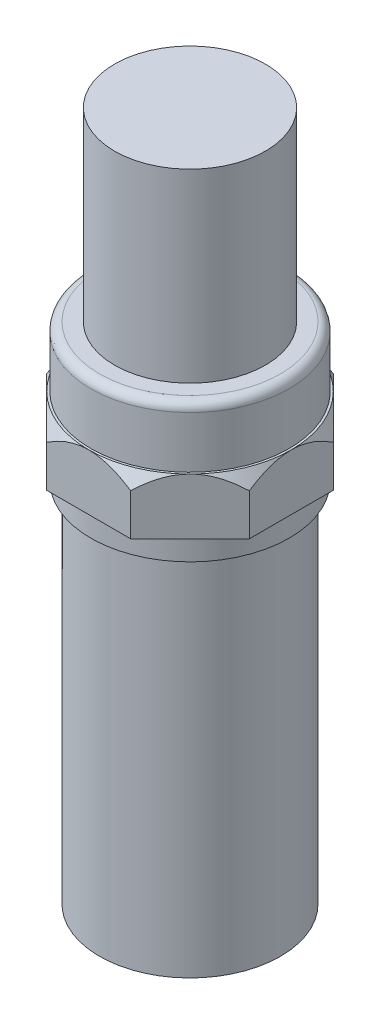
SolidWorks part; units mm, degrees
ref_plane "Front Plane" through (0, 0, 0) normal (0, 0, 1) x (1, 0, 0)
ref_plane "Top Plane" through (0, 0, 0) normal (0, 1, 0) x (1, 0, 0)
ref_plane "Right Plane" through (0, 0, 0) normal (1, 0, 0) x (0, 0, -1)
sketch "Sketch1" plane through (0, 0, 0) normal (0, 1, 0) x (1, 0, 0)
  circle A0 centre (0, 0) radius 20
  dimension "D1" = 40
extrude "Extrude-Thin1" add sketch "Sketch1" along normal blind 85 thin
sketch "Sketch2" plane through (0, 85, 0) normal (0, 1, 0) x (1, 0, 0)
  circle A0 centre (0, 0) radius 21
  circle A1 centre (0, 0) radius 21 construction
extrude "Extrude-Thin2" add sketch "Sketch2" along normal blind 5 separate body thin
sketch "Sketch3" plane through (0, 90, 0) normal (0, 1, 0) x (1, 0, 0)
  line L1 (-23.5, -9.734) -> (-9.734, -23.5)
  line L2 (-9.734, -23.5) -> (9.734, -23.5)
  line L3 (9.734, -23.5) -> (23.5, -9.734)
  line L4 (23.5, -9.734) -> (23.5, 9.734)
  line L5 (23.5, 9.734) -> (9.734, 23.5)
  line L6 (9.734, 23.5) -> (-9.734, 23.5)
  line L7 (-9.734, 23.5) -> (-23.5, 9.734)
  line L8 (-23.5, 9.734) -> (-23.5, -9.734)
  circle A0 centre (0, 0) radius 23.5 construction
  circle A1 centre (0, 0) radius 23
  circle A2 centre (0, 0) radius 23 construction
  dimension "D1" = 47
extrude "Extrude1" add sketch "Sketch3" along normal blind 13 separate body
sketch "Sketch5" plane through (0, 0, 0) normal (0, 0, 1) x (1, 0, 0)
  line L0 (26.3868, 103) -> (26.3868, 98)
  line L2 (23.5, 103) -> (26.3868, 98)
  line L3 (23.5, 103) -> (26.3868, 103)
  dimension "D1" = 60
  dimension "D2" = 5
sketch "Sketch6" plane through (0, 103, 0) normal (0, 1, 0) x (1, 0, 0)
  circle A0 centre (0, 0) radius 30
sweep "Cut-Sweep2" cut profiles "Sketch5" path "Sketch6"
sketch "Sketch7" plane through (0, 103, 0) normal (0, 1, 0) x (1, 0, 0)
  circle A0 centre (0, 0) radius 23
  circle A1 centre (0, 0) radius 23 construction
extrude "Extrude3" add sketch "Sketch7" along normal blind 14 separate body
sketch "Sketch11" plane through (0, 117, 0) normal (0, 1, 0) x (1, 0, 0)
  circle A0 centre (0, 0) radius 2
  dimension "D1" = 4
extrude "Extrude5" add sketch "Sketch11" along normal blind 30
sketch "Sketch12" plane through (0, 147, 0) normal (0, 1, 0) x (1, 0, 0)
  circle A0 centre (0, 0) radius 12.5
  dimension "D1" = 25
extrude "Extrude6" add sketch "Sketch12" along normal blind 3
sketch "Sketch9" plane through (0, 117, 0) normal (0, 1, 0) x (1, 0, 0)
  circle A0 centre (0, 0) radius 17.5
  dimension "D1" = 35
extrude "Extrude4" add sketch "Sketch9" along normal blind 43 separate body
fillet "Fillet1" radius 2 1 edges at (0, 117, 23)
sketch "Sketch10" plane through (0, 0, 0) normal (1, 0, 0) x (0, 0, -1)
  line L0 (0, 625.4381) -> (0, -391.4381)
  line L1 (0, 625.4381) -> (0, -391.4381) construction
  line L2 (0, 0) -> (0, 117) construction
  line L3 (21, 117) -> (-21, 117) construction
  arc A0 (0, 625.4381) -> (0, -391.4381) centre (-39.8837, 117) ccw
  dimension "D1" = 1020
revolve "485" [suppressed] add sketch "Sketch10" angle 360 about L1
sketch "Cutting Hole" plane through (0, 0, 0) normal (0, -1, 0) x (1, 0, 0)
  circle A0 centre (0, 0) radius 20
  dimension "D1" = 40
